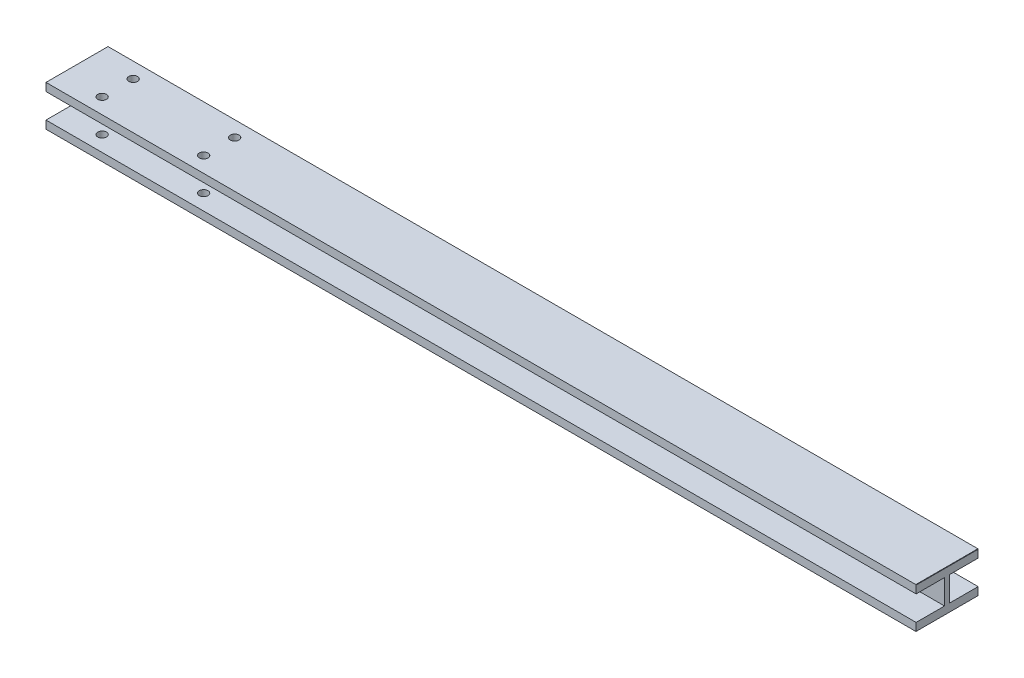
SolidWorks part; units mm, degrees
ref_plane "前视基准面" through (0, 0, 0) normal (0, 0, 1) x (1, 0, 0)
ref_plane "上视基准面" through (0, 0, 0) normal (0, 1, 0) x (1, 0, 0)
ref_plane "右视基准面" through (0, 0, 0) normal (1, 0, 0) x (0, 0, -1)
other "Configuration Table"
sketch "Sketch1" plane through (0, 0, 0) normal (0, 1, 0) x (1, 0, 0)
  line L0 (-1000, -106.95) -> (49000, -106.95) construction
  line L1 (0, 0) -> (3000, 0)
  line L2 (0, 0) -> (0, -213.9)
  line L3 (0, -213.9) -> (3000, -213.9)
  line L4 (3000, 0) -> (3000, -213.9)
  line L5 (140, -53.475) -> (490, -53.475) construction
  line L6 (140, 0) -> (140, -106.95) construction
  circle A0 centre (140, -53.475) radius 15
  circle A1 centre (140, -160.425) radius 15
  circle A2 centre (490, -53.475) radius 15
  circle A3 centre (490, -160.425) radius 15
  point P7 (0, -106.95)
  point P18 (140, -53.475)
  dimension "30" = 30
  dimension "D4" = 30
  dimension "D7" = 140
  dimension "D1" = 3000
  dimension "D2" = 213.9
  dimension "D5" = 350
extrude "Boss-Extrude1" add sketch "Sketch1" along normal blind 140
sketch "Sketch2" plane through (0, 0, 0) normal (0, -1, 0) x (1, 0, 0)
  line L0 (1213.9, 106.95) -> (51213.9, 106.95) construction
  line L1 (3000, 213.9) -> (3000, 0) construction
  line L3 (3000, 109.95) -> (2997, 109.95)
  line L4 (3000, 109.95) -> (3000, 103.95)
  line L5 (3000, 103.95) -> (2997, 103.95)
  line L6 (2997, 109.95) -> (2997, 103.95)
  point P5 (3000, 106.95)
  point P9 (2997, 106.95)
  dimension "D1" = 3
  dimension "D2" = 6
extrude "Cut-Extrude1" cut sketch "Sketch2" against normal blind 0.1
sketch "Sketch4" plane through (3000, 0, 0) normal (1, 0, 0) x (0, 0, -1)
  line L0 (-213.9, 140) -> (0, 140) construction
  line L1 (-106.95, 140) -> (-106.95, -8.9763) construction
  line L2 (-213.9, 112.5) -> (-115.9, 112.5)
  line L3 (-213.9, 140) -> (-213.9, 0) construction
  line L4 (0, 112.5) -> (-98, 112.5)
  line L5 (-115.9, 112.5) -> (-115.9, 27.5)
  line L6 (-98, 112.5) -> (-98, 27.5)
  line L7 (-115.9, 27.5) -> (-213.9, 27.5)
  line L8 (-98, 27.5) -> (0, 27.5)
  line L9 (-213.9, 27.5) -> (-213.9, 112.5)
  line L10 (0, 27.5) -> (0, 112.5)
  line L11 (-213.9, 140) -> (-213.9, 112.5)
  line L12 (0, 140) -> (0, 112.5)
  line L13 (-213.9, 27.5) -> (-213.9, 0)
  line L14 (0, 27.5) -> (0, 0)
  line M10 (-213.9, 140) -> (-213.9, 0)
  line M16 (0, 0) -> (0, 140)
  dimension "D1" = 98
  dimension "D2" = 85
extrude "Cut-Extrude3" cut sketch "Sketch4" against normal through all contours L7 L5 L2 M10 | L6 L8 L4 M16
sketch "Sketch5" plane through (0, 140, 0) normal (0, 1, 0) x (1, 0, 0)
  line L0 (0, -213.9) -> (3000, -213.9) construction
  line L1 (3000, 0) -> (2999, 0)
  line L2 (3000, 0) -> (3000, -213.9)
  line L3 (3000, -213.9) -> (2999, -213.9)
  line L4 (2999, 0) -> (2999, -213.9)
  dimension "D1" = 1
extrude "Cut-Extrude4" cut sketch "Sketch5" against normal blind 1
sketch "Sketch6" plane through (0, 0, 0) normal (0, 0, -1) x (-1, 0, 0)
  line L0 (0, 0) -> (-3000, 0) construction
  line L1 (-3000, 139) -> (-2999.5, 139)
  line L2 (-3000, 139) -> (-3000, 0)
  line L3 (-3000, 0) -> (-2999.5, 0)
  line L4 (-2999.5, 139) -> (-2999.5, 0)
  dimension "D1" = 0.5
extrude "Cut-Extrude5" cut sketch "Sketch6" against normal blind 0.5
sketch "Sketch7" plane through (0, 0, 0) normal (0, -1, 0) x (1, 0, 0)
  line L0 (0, 0) -> (3000, 0) construction
  line L1 (3000, 213.9) -> (2999, 213.9)
  line L2 (3000, 213.9) -> (3000, 0)
  line L3 (3000, 0) -> (2999, 0)
  line L4 (2999, 213.9) -> (2999, 0)
  dimension "D1" = 1
extrude "Cut-Extrude6" cut sketch "Sketch7" against normal blind 0.5
